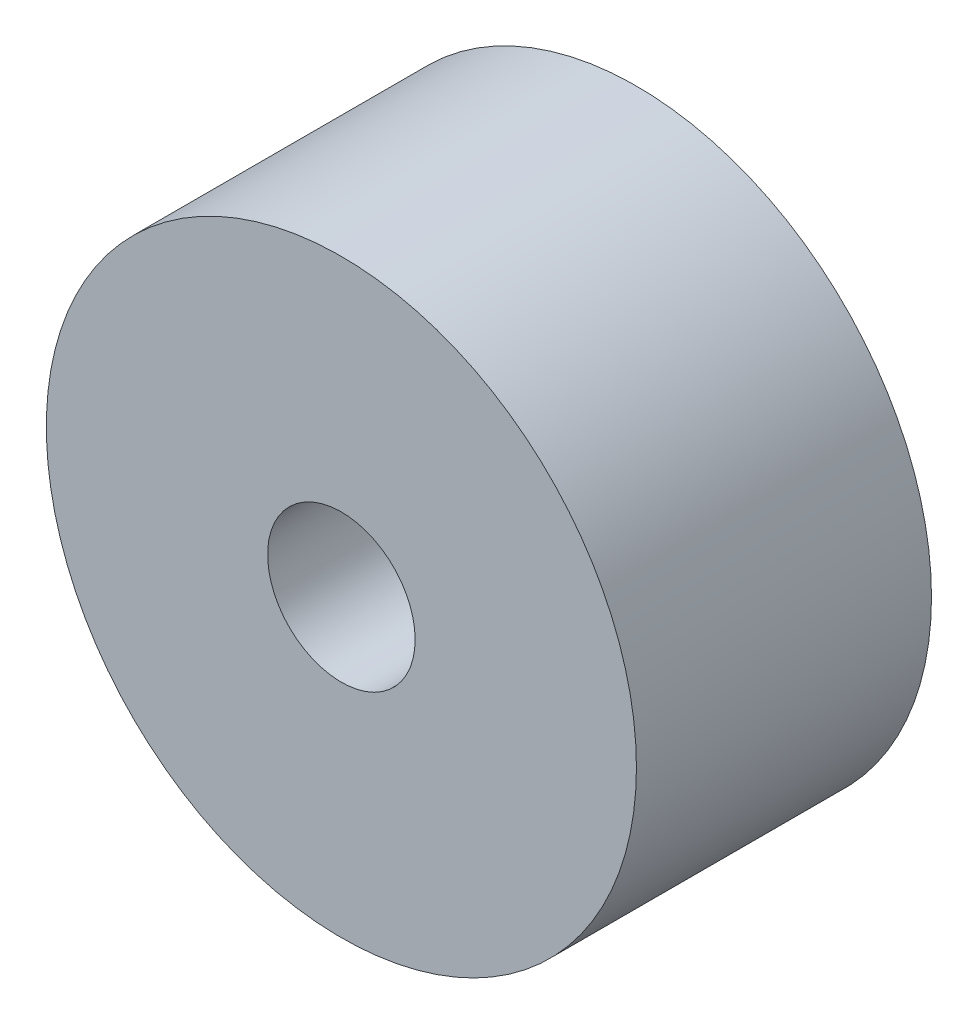
SolidWorks part; units mm, degrees
ref_plane "Front Plane" through (0, 0, 0) normal (0, 0, 1) x (1, 0, 0)
ref_plane "Top Plane" through (0, 0, 0) normal (0, 1, 0) x (1, 0, 0)
ref_plane "Right Plane" through (0, 0, 0) normal (1, 0, 0) x (0, 0, -1)
sketch "Sketch1" plane through (0, 0, 0) normal (0, 0, 1) x (1, 0, 0)
  circle A0 centre (0, 0) radius 12.7
  circle A1 centre (0, 0) radius 3.175
  dimension "D1" = 6.35
  dimension "D2" = 25.4
extrude "Boss-Extrude1" add sketch "Sketch1" along normal blind 12.7
